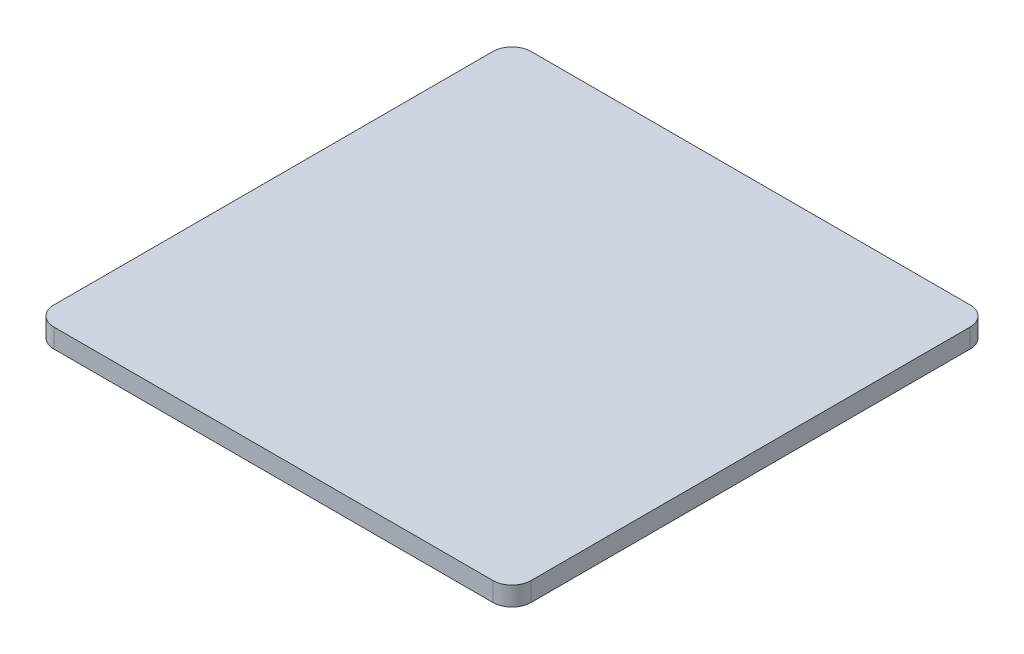
SolidWorks part; units mm, degrees
material "Oak"
ref_plane "Front" through (0, 0, 0) normal (0, 0, 1) x (1, 0, 0)
ref_plane "Top" through (0, 0, 0) normal (0, 1, 0) x (1, 0, 0)
ref_plane "Right" through (0, 0, 0) normal (1, 0, 0) x (0, 0, -1)
sketch "Sketch1" plane through (0, 0, 0) normal (0, 1, 0) x (1, 0, 0)
  line L1 (63.5, -63.5) -> (-63.5, -63.5)
  line L2 (63.5, -63.5) -> (63.5, 63.5)
  line L3 (63.5, 63.5) -> (-63.5, 63.5)
  line L4 (-63.5, -63.5) -> (-63.5, 63.5)
  line L5 (63.5, -63.5) -> (-63.5, 63.5) construction
  line L6 (63.5, 63.5) -> (-63.5, -63.5) construction
  point P0 (0, 0)
  dimension "D1" = 127
extrude "Boss-Extrude1" add sketch "Sketch1" along normal blind 5.08
fillet "Fillet1" radius 5.08 4 edges at (-63.5, 2.54, -63.5) (63.5, 2.54, -63.5) (-63.5, 2.54, 63.5) (63.5, 2.54, 63.5)
